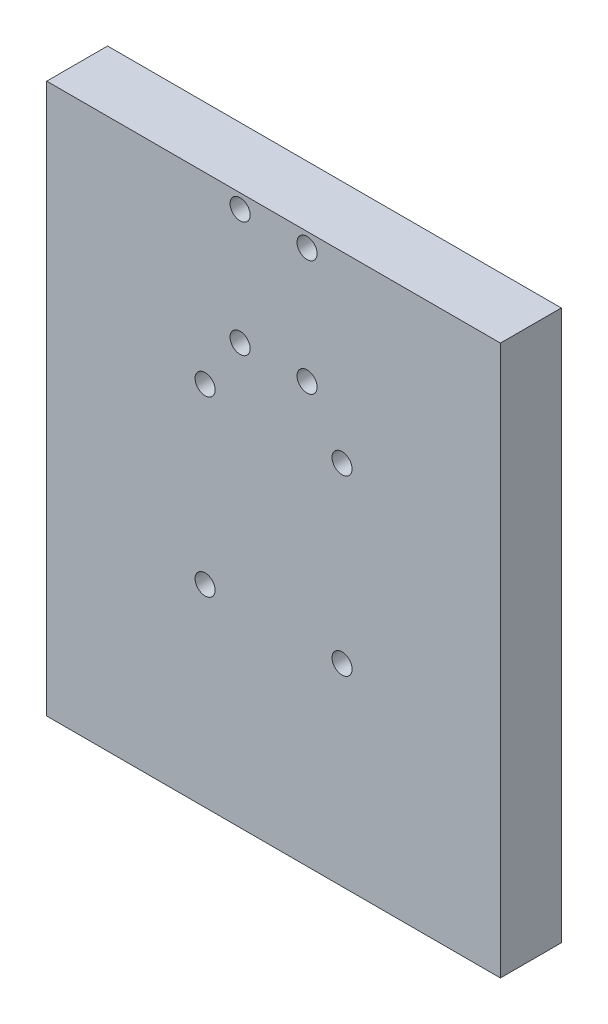
SolidWorks part; units mm, degrees
ref_plane "Front Plane" through (0, 0, 0) normal (0, 0, 1) x (1, 0, 0)
ref_plane "Top Plane" through (0, 0, 0) normal (0, 1, 0) x (1, 0, 0)
ref_plane "Right Plane" through (0, 0, 0) normal (1, 0, 0) x (0, 0, -1)
sketch "Sketch1" plane through (0, 0, 0) normal (0, 0, 1) x (1, 0, 0)
  line L0 (-126.9886, 2186.5486) -> (-126.9886, 2394.0828) construction
  line L1 (-52.4383, 2367.2486) -> (-201.5388, 2367.2486)
  line L2 (-201.5388, 2367.2486) -> (-201.5388, 2186.5486)
  line L3 (-201.5388, 2186.5486) -> (-52.4383, 2186.5486)
  line L4 (-52.4383, 2367.2486) -> (-52.4383, 2186.5486)
  point P7 (-126.9886, 2367.2486)
extrude "Boss-Extrude1" add sketch "Sketch1" along normal blind 20
hole_wizard "M6 Clearance Hole1" positions "Sketch2" profile "Sketch3" hole size "M6" standard "ISO"
sketch "Sketch2" plane through (0, 0, 20) normal (0, 0, 1) x (1, 0, 0)
  point P0 (-149.4886, 2307.0486)
  point P2 (-104.4886, 2307.0486)
  point P4 (-104.4886, 2250.0486)
  point P6 (-149.4886, 2250.0486)
  point P8 (-137.9886, 2362.5486)
  point P10 (-137.9886, 2324.5486)
  point P12 (-115.9886, 2324.5486)
  point P14 (-115.9886, 2362.5486)
sketch "Sketch3" plane through (-149.4886, 2307.0486, 20) normal (1, 0, 0) x (0, -1, 0)
  line L0 (0, 0) -> (0, 38.5828)
  line L1 (0, 38.5828) -> (3.3, 36.6)
  line L2 (3.3, 36.6) -> (3.3, 0)
  line L5 (3.3, 0) -> (0, 0)
  line L10 (0, 38.5828) -> (-3.3, 36.6) construction
  line L11 (0, -6.35) -> (0, 107.95) construction
  dimension "Hole Dia." = 6.6
  dimension "Hole Depth" = 36.6
  dimension "Drill Angle" = 118
